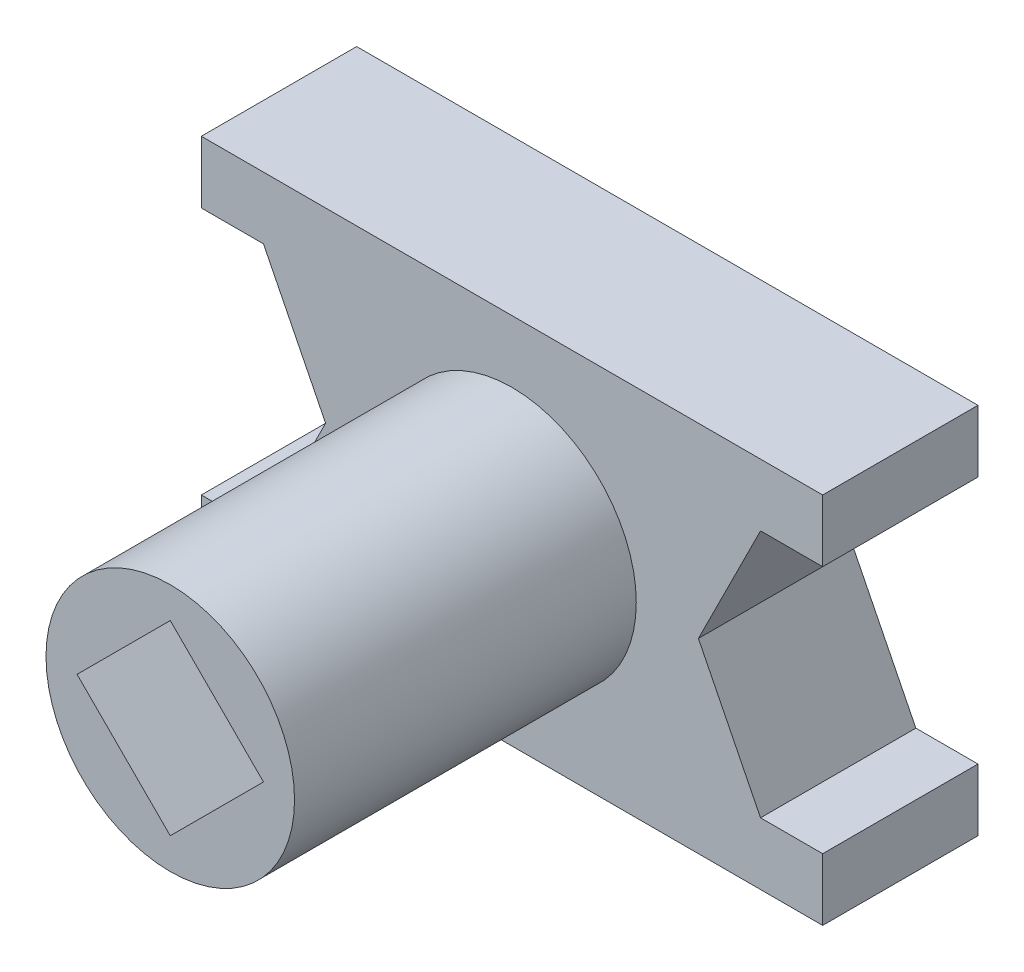
SolidWorks part; units mm, degrees
ref_plane "Спереди" through (0, 0, 0) normal (0, 0, 1) x (1, 0, 0)
ref_plane "Сверху" through (0, 0, 0) normal (0, 1, 0) x (1, 0, 0)
ref_plane "Справа" through (0, 0, 0) normal (1, 0, 0) x (0, 0, -1)
sketch "Эскиз1" plane through (0, 0, 0) normal (0, 0, 1) x (1, 0, 0)
  line L0 (0, 0) -> (-50, 0) construction
  line L1 (50, -30) -> (-50, -30)
  line L2 (50, -30) -> (50, -20)
  line L3 (50, 30) -> (-50, 30)
  line L4 (-50, -30) -> (-50, -20)
  line L5 (50, -30) -> (-50, 30) construction
  line L6 (50, 30) -> (-50, -30) construction
  line L7 (-50, 20) -> (-40, 20)
  line L8 (-40, 20) -> (-30, 0)
  line L9 (-40, -20) -> (-30, 0)
  line L10 (-50, -20) -> (-40, -20)
  line L11 (0, 0) -> (0, 30) construction
  line L12 (50, -20) -> (40, -20)
  line L13 (40, -20) -> (30, 0)
  line L14 (40, 20) -> (30, 0)
  line L15 (50, 20) -> (40, 20)
  line L16 (-50, 20) -> (-50, 30)
  line L17 (50, 20) -> (50, 30)
  point P0 (0, 0)
  dimension "D1" = 100
  dimension "D2" = 60
  dimension "D3" = 10
  dimension "D4" = 10
  dimension "D5" = 10
extrude "Бобышка-Вытянуть1" add sketch "Эскиз1" along normal blind 25
sketch "Эскиз2" plane through (0, 0, 25) normal (0, 0, 1) x (1, 0, 0)
  circle A0 centre (0, 0) radius 20
  dimension "D1" = 40
extrude "Бобышка-Вытянуть2" add sketch "Эскиз2" along normal blind 55
sketch "Эскиз3" plane through (0, 0, 80) normal (0, 0, 1) x (1, 0, 0)
  line L0 (0, 0) -> (-10.6066, 10.6066) construction
  line L1 (0, 0) -> (-15, 0) construction
  line L3 (15, 0) -> (0, -15)
  line L4 (15, 0) -> (0, 15)
  line L5 (0, 15) -> (-15, 0)
  line L6 (0, -15) -> (-15, 0)
  line L7 (10.6066, -10.6066) -> (-10.6066, 10.6066) construction
  line L8 (10.6066, 10.6066) -> (-10.6066, -10.6066) construction
  circle A0 centre (0, 0) radius 15 construction
  dimension "D1" = 30
  dimension "D2" = 45
extrude "Вырез-Вытянуть1" cut sketch "Эскиз3" against normal blind 40
sketch "Эскиз4" plane through (0, 0, 40) normal (0, 0, 1) x (1, 0, 0)
  circle A0 centre (0, 0) radius 8
  dimension "D1" = 16
extrude "Вырез-Вытянуть2" cut sketch "Эскиз4" against normal blind 40
